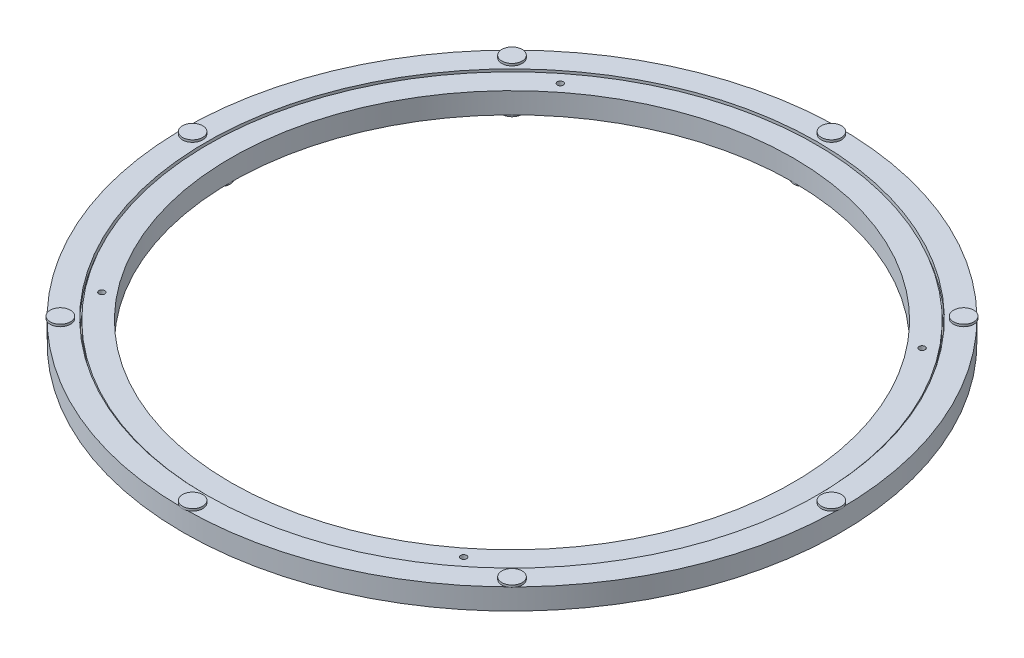
SolidWorks part; units mm, degrees
ref_plane "Front Plane" through (0, 0, 0) normal (0, 0, 1) x (1, 0, 0)
ref_plane "Top Plane" through (0, 0, 0) normal (0, 1, 0) x (1, 0, 0)
ref_plane "Right Plane" through (0, 0, 0) normal (1, 0, 0) x (0, 0, -1)
sketch "Sketch1" plane through (0, 0, 0) normal (0, 1, 0) x (1, 0, 0)
  line L0 (0, 221) -> (0, -221) construction
  line L1 (-221, 0) -> (221, 0) construction
  line L2 (154.0878, 121.6168) -> (0, 0) construction
  circle A0 centre (0, 0) radius 189
  circle A1 centre (0, 0) radius 221
  circle A2 centre (0, 0) radius 214.7 construction
  circle A3 centre (0, 0) radius 196.3 construction
  circle A4 centre (0, 214.7) radius 6.8
  circle A5 centre (0, 214.7) radius 3.05
  circle A6 centre (0, 196.3) radius 3.05
  circle A7 centre (0, 196.3) radius 6.8
  circle A8 centre (151.8158, 151.8158) radius 3.05
  circle A9 centre (214.7, 0) radius 3.05
  circle A10 centre (151.8158, -151.8158) radius 3.05
  circle A11 centre (0, -214.7) radius 3.05
  circle A12 centre (-151.8158, -151.8158) radius 3.05
  circle A17 centre (138.8051, 138.8051) radius 3.05
  circle A18 centre (196.3, 0) radius 3.05
  circle A19 centre (138.8051, -138.8051) radius 3.05
  circle A20 centre (0, -196.3) radius 3.05
  circle A21 centre (-138.8051, -138.8051) radius 3.05
  circle A24 centre (154.0878, 121.6168) radius 2
  circle A25 centre (121.6168, -154.0878) radius 2
  circle A26 centre (-154.0878, -121.6168) radius 2
  circle A27 centre (-121.6168, 154.0878) radius 2
  circle A54 centre (-214.7, 0) radius 3.05
  circle A55 centre (-151.8158, 151.8158) radius 3.05
  circle A56 centre (-196.3, 0) radius 3.05
  circle A57 centre (-138.8051, 138.8051) radius 3.05
  point P28 (155.6577, 122.8559)
  point P36 (0, 0)
  point P38 (0, 189)
  point P39 (0, 217.75)
  point P51 (0, 0)
  point P52 (0, 221.5)
  point P61 (0, 0)
  point P62 (0, 193.25)
  point P63 (0, 189.5)
  dimension "ID" = 378
  dimension "OD" = 442
  dimension "Outer Ring Dia" = 429.4
  dimension "Inner Ring Dia" = 392.6
  dimension "Bumper Hole Dia" = 6.1
  dimension "Bumper Dia" = 13.6
  dimension "Mounting Hole Dia" = 4
  dimension "D1" = 23
  dimension "No. Outside Bumpers" = 8
  dimension "No. Inside Bumpers" = 8
  dimension "No. Mounting Holes" = 4
sketch "Sketch2" plane through (0, 0, 0) normal (1, 0, 0) x (0, 0, -1)
  line L0 (205, 7.55) -> (205, -7.55) construction
  line L1 (189, -7.55) -> (189, 6.55)
  line L2 (189, 6.55) -> (204.5, 6.55)
  line L4 (204.5, -7.55) -> (189, -7.55)
  line L5 (221, 7.55) -> (205.5, 7.55)
  line L7 (205.5, -6.55) -> (221, -6.55)
  line L8 (221, -6.55) -> (221, 7.55)
  line L9 (204.5, 6.55) -> (204.5, -7.55)
  line L10 (193.25, -1.05) -> (196.3, -1.05)
  line L12 (205.5, 7.55) -> (205.5, -6.55)
  line L13 (189, 6.55) -> (221, -6.55) construction
  line L14 (221, 0) -> (-221, 0) construction
  line L15 (0, 7.55) -> (0, -7.55) construction
  line L16 (214.7, -6.55) -> (214.7, 9.017) construction
  line L18 (196.3, 6.55) -> (196.3, -9.017) construction
  line L19 (214.7, 9.017) -> (221.5, 9.017)
  line L20 (221.5, 9.017) -> (221.5, 7.55)
  line L21 (217.75, 7.55) -> (217.75, 1.05)
  line L22 (217.75, 1.05) -> (214.7, 1.05)
  line L23 (196.3, -9.017) -> (189.5, -9.017)
  line L24 (189.5, -9.017) -> (189.5, -7.55)
  line L25 (193.25, -7.55) -> (193.25, -1.05)
  line L27 (193.25, -7.55) -> (196.3, -7.55)
  circle A0 centre (205, 0) radius 3.9687
  dimension "D4" = 7.9375
  dimension "Height" = 15.1
  dimension "D3" = 1
  dimension "D5" = 6.5
  dimension "D1" = 1
  dimension "D2" = 6.5
  dimension "OA Height" = 18.034
sketch "Sketch4" plane through (0, 0, 0) normal (1, 0, 0) x (0, 0, -1)
  line L0 (204.5, 6.55) -> (204.5, -7.55) construction
  line L1 (189, 6.55) -> (204.5, 6.55) construction
  line L2 (189, -7.55) -> (189, 6.55) construction
  line L3 (204.5, -7.55) -> (189, -7.55) construction
  line L4 (204.5, 6.55) -> (204.5, 3.9371)
  line L5 (189, 6.55) -> (204.5, 6.55)
  line L6 (189, -7.55) -> (189, 6.55)
  line L7 (204.5, -7.55) -> (189, -7.55)
  line L8 (221, -6.55) -> (221, 7.55) construction
  line L9 (205.5, -6.55) -> (221, -6.55) construction
  line L10 (205.5, 7.55) -> (205.5, -6.55) construction
  line L11 (221, 7.55) -> (205.5, 7.55) construction
  line L12 (221, -6.55) -> (221, 7.55)
  line L13 (205.5, -6.55) -> (221, -6.55)
  line L14 (205.5, 7.55) -> (205.5, 3.9371)
  line L15 (221, 7.55) -> (205.5, 7.55)
  line L16 (205.5, -3.9371) -> (205.5, -6.55)
  line L17 (204.5, -3.9371) -> (204.5, -7.55)
  circle A0 centre (205, 0) radius 3.9687 construction
  arc A1 (204.5, 3.9371) -> (204.5, -3.9371) centre (205, 0) ccw
  arc A2 (205.5, -3.9371) -> (205.5, 3.9371) centre (205, 0) ccw
revolve "Revolve1" add sketch "Sketch4" angle 360 about L15
sketch "Sketch6" plane through (0, 0, 0) normal (0, 1, 0) x (1, 0, 0)
  circle A0 centre (154.0878, 121.6168) radius 2 construction
  circle A1 centre (154.0878, 121.6168) radius 2
extrude "Cut-Extrude2" cut sketch "Sketch6" against normal through all both and the other way through all
pattern_circular "CirPattern1" count 4 over 360 about axis through (0, 0, 0) along (0, 1, 0) of "Cut-Extrude2"
sketch "Sketch7" plane through (0, 7.55, 0) normal (0, 1, 0) x (1, 0, 0)
  circle A0 centre (0, 214.7) radius 3.05 construction
  circle A1 centre (0, 214.7) radius 3.05
extrude "Cut-Extrude3" cut sketch "Sketch7" against normal up to vertex (6.5 mm away) up to point (0, 1.05, -217.75)
pattern_circular "CirPattern2" count 8 over 360 about axis through (0, 0, 0) along (0, 1, 0) of "Cut-Extrude3"
sketch "Sketch8" plane through (0, -7.55, 0) normal (0, 1, 0) x (1, 0, 0)
  circle A0 centre (0, 196.3) radius 3.05 construction
  circle A1 centre (0, 196.3) radius 3.05
extrude "Cut-Extrude4" cut sketch "Sketch8" along normal up to vertex (6.5 mm away) up to point (0, -1.05, -193.25)
pattern_circular "CirPattern3" count 8 over 360 about axis through (0, 0, 0) along (0, 1, 0) of "Cut-Extrude4"
sketch "Sketch9" plane through (0, 0, 0) normal (1, 0, 0) x (0, 0, -1)
  line L0 (214.7, -6.55) -> (214.7, 9.017) construction
  line L1 (214.7, 9.017) -> (221.5, 9.017) construction
  line L2 (221.5, 9.017) -> (221.5, 7.55) construction
  line L3 (221, 7.55) -> (205.5, 7.55) construction
  line L4 (217.75, 7.55) -> (217.75, 1.05) construction
  line L6 (214.7, 1.05) -> (214.7, 9.017)
  line L7 (214.7, 9.017) -> (221.5, 9.017)
  line L8 (221.5, 9.017) -> (221.5, 7.55)
  line L9 (221.5, 7.55) -> (217.75, 7.55)
  line L10 (217.75, 7.55) -> (217.75, 1.05)
  line L12 (217.75, 1.05) -> (214.7, 1.05) construction
  line L13 (217.75, 1.05) -> (214.7, 1.05)
revolve "Revolve2" add sketch "Sketch9" angle 360 about L16
pattern_circular "CirPattern4" count 8 over 360 about axis through (0, 0, 0) along (0, 1, 0) of bodies 113
sketch "Sketch10" plane through (0, 0, 0) normal (1, 0, 0) x (0, 0, -1)
  line L2 (204.5, -7.55) -> (189, -7.55) construction
  line L3 (189.5, -9.017) -> (189.5, -7.55) construction
  line L4 (196.3, -9.017) -> (189.5, -9.017) construction
  line L7 (193.25, -7.55) -> (189.5, -7.55)
  line L8 (189.5, -9.017) -> (189.5, -7.55)
  line L9 (196.3, -9.017) -> (189.5, -9.017)
  line L10 (196.3, 6.55) -> (196.3, -9.017) construction
  line L11 (196.3, -1.05) -> (196.3, -9.017)
  line L12 (193.25, -1.05) -> (196.3, -1.05) construction
  line L13 (193.25, -7.55) -> (193.25, -1.05) construction
  line L14 (193.25, -1.05) -> (196.3, -1.05)
  line L15 (193.25, -7.55) -> (193.25, -1.05)
revolve "Revolve3" add sketch "Sketch10" angle 360 about L18
pattern_circular "CirPattern5" count 8 over 360 about axis through (0, 0, 0) along (0, 1, 0) of bodies 114
sketch "Drawing Ref" plane through (0, 0, 0) normal (1, 0, 0) x (0, 0, -1)
  line L0 (0, 7.55) -> (0, -7.55) construction
  line L1 (0, 7.55) -> (0, -7.55) construction
  line L2 (189, 7.55) -> (189, -6.55)
  line L3 (205.5, -6.55) -> (221, -6.55) construction
  line L4 (221, 7.55) -> (205.5, 7.55) construction
  line L5 (189, -7.55) -> (189, 6.55) construction
  line L6 (221.5, 9.017) -> (221.5, -9.017) construction
  line L8 (-189, 7.55) -> (-189, -6.55)
  line L9 (-221.5, 9.017) -> (-221.5, -9.017) construction
  line L10 (196.3, -9.017) -> (189.5, -9.017) construction
equation "\"D1@CirPattern1\"=\"No. Mounting Holes@Sketch1\""
equation "\"D1@CirPattern2\"=\"No. Outside Bumpers@Sketch1\""
equation "\"D1@CirPattern3\"=\"No. Inside Bumpers@Sketch1\""
equation "\"D1@CirPattern4\"=\"No. Outside Bumpers@Sketch1\""
equation "\"D1@CirPattern5\"=\"No. Inside Bumpers@Sketch1\""
equation "\"D2@Sketch2\"=\"D5@Sketch2\""
